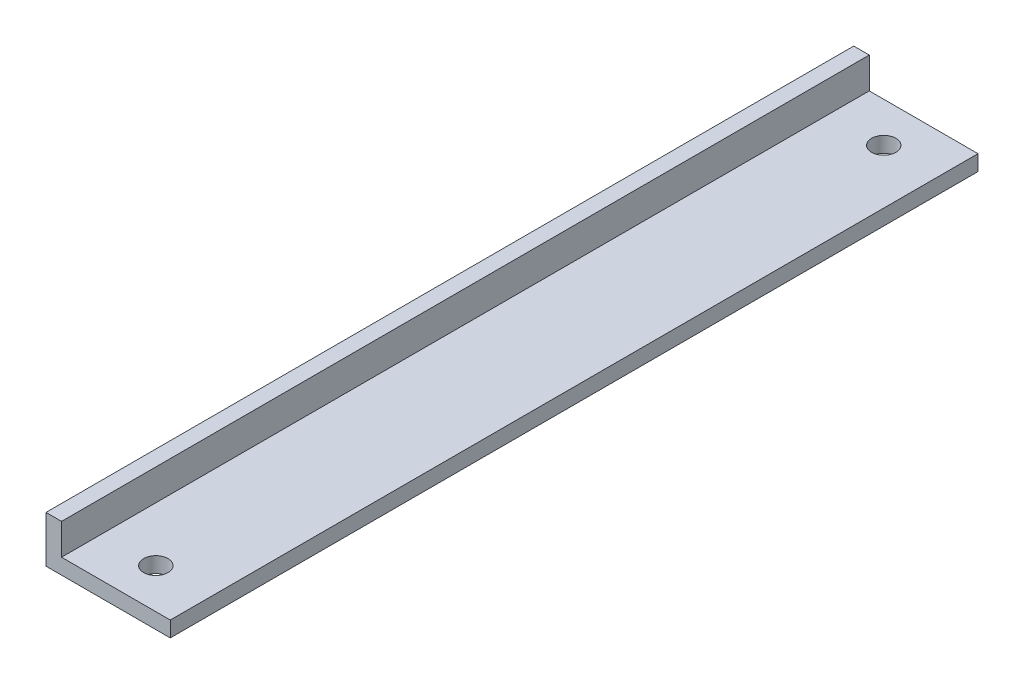
SolidWorks part; units mm, degrees
ref_plane "Front Plane" through (0, 0, 0) normal (0, 0, 1) x (1, 0, 0)
ref_plane "Top Plane" through (0, 0, 0) normal (0, 1, 0) x (1, 0, 0)
ref_plane "Right Plane" through (0, 0, 0) normal (1, 0, 0) x (0, 0, -1)
sketch "Sketch1" plane through (0, 0, 0) normal (0, 0, 1) x (1, 0, 0)
  line L0 (0, 0) -> (25.4, 0)
  line L1 (25.4, 0) -> (25.4, 3.175)
  line L2 (25.4, 3.175) -> (3.175, 3.175)
  line L3 (3.175, 3.175) -> (3.175, 25.4)
  line L4 (3.175, 25.4) -> (0, 25.4)
  line L5 (0, 25.4) -> (0, 0)
  line L6 (0, 9.525) -> (3.175, 9.525)
  dimension "D1" = 25.4
  dimension "D2" = 3.175
  dimension "D3" = 6.35
extrude "Boss-Extrude1" add sketch "Sketch1" along normal mid plane 165.1 contours L6 L5 L0 L1 L2 L3
sketch "Sketch2" plane through (0, 0, 0) normal (0, 1, 0) x (1, 0, 0)
  line L0 (14.2875, 74.3926) -> (14.2875, 82.55) construction
  line L1 (14.2875, 74.3926) -> (14.2875, -74.3926) construction
  line L2 (25.4, 82.55) -> (3.175, 82.55) construction
  line L4 (14.2875, -74.3926) -> (14.2875, -82.55) construction
  line L5 (25.4, -82.55) -> (3.175, -82.55) construction
  circle A1 centre (14.2875, -74.3926) radius 2.4892
  circle A2 centre (14.2875, 74.3926) radius 2.4892
  point P2 (14.2875, 0)
  dimension "D1" = 4.9784
  dimension "D2" = 4.9784
  dimension "D4" = 148.7852
extrude "Cut-Extrude4" cut sketch "Sketch2" along normal through all
